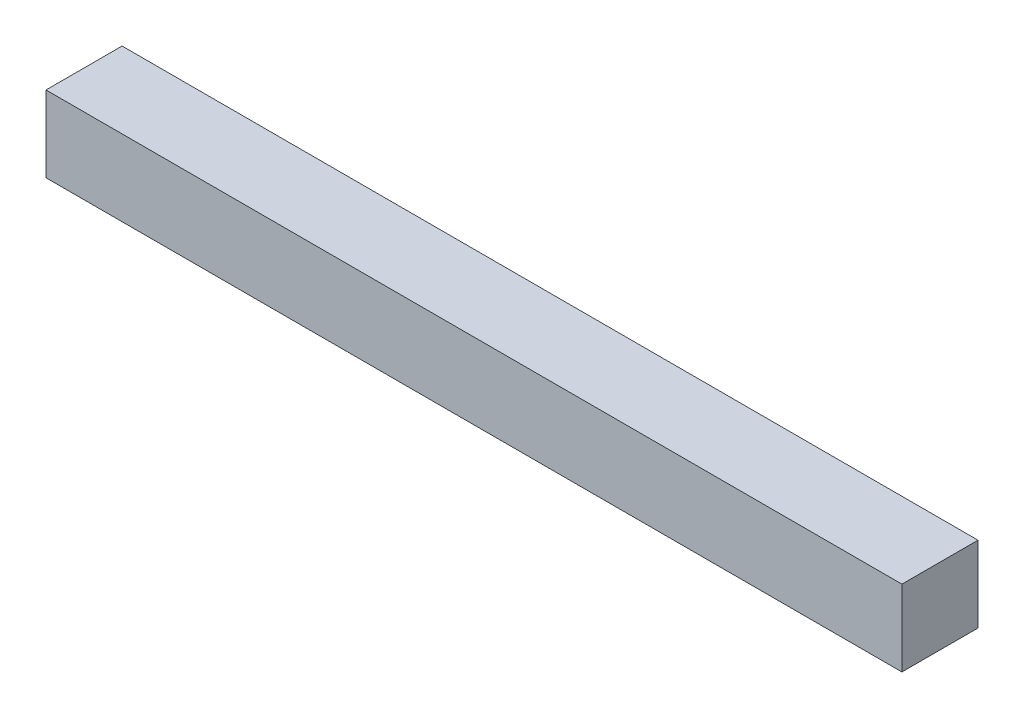
SolidWorks part; units mm, degrees
ref_plane "前视基准面" through (0, 0, 0) normal (0, 0, 1) x (1, 0, 0)
ref_plane "上视基准面" through (0, 0, 0) normal (0, 1, 0) x (1, 0, 0)
ref_plane "右视基准面" through (0, 0, 0) normal (1, 0, 0) x (0, 0, -1)
sketch "草图1" plane through (0, 0, 0) normal (0, 1, 0) x (1, 0, 0)
  line L1 (0, 0) -> (27, 0)
  line L2 (0, 0) -> (0, 2.4)
  line L3 (0, 2.4) -> (27, 2.4)
  line L4 (27, 0) -> (27, 2.4)
  dimension "D1" = 27
  dimension "D2" = 2.4
extrude "凸台-拉伸1" add sketch "草图1" along normal blind 2.4
